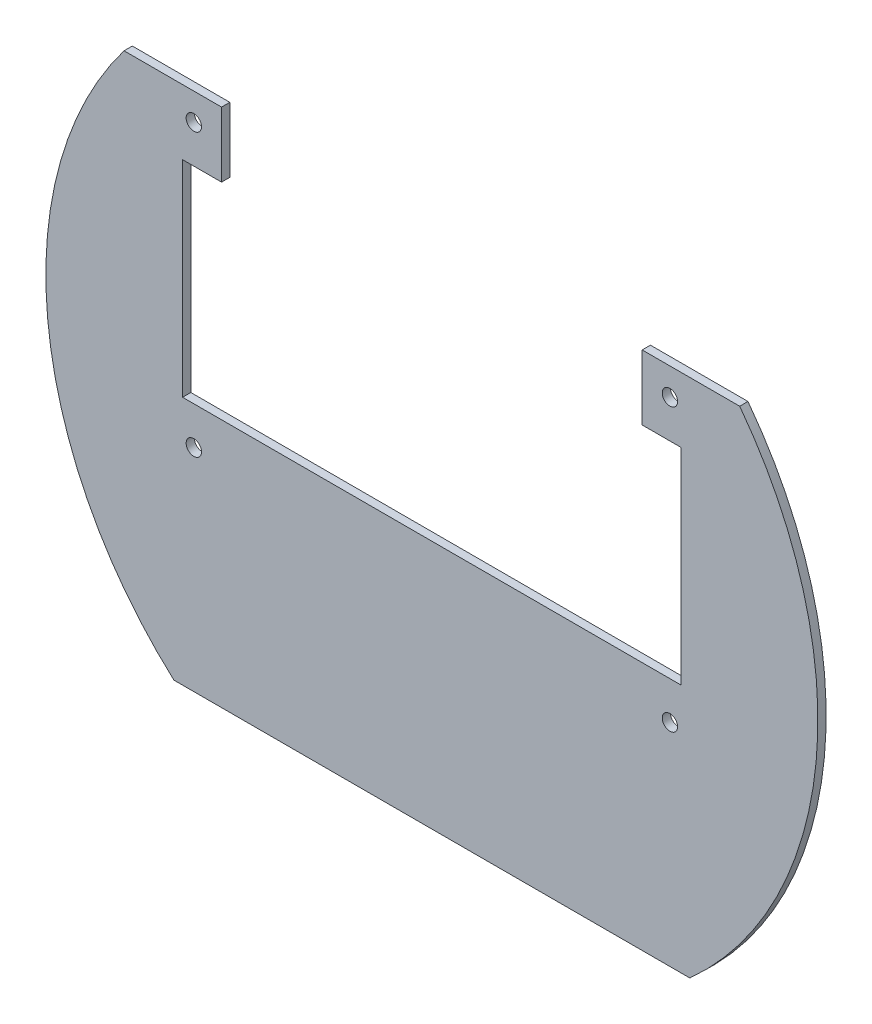
SolidWorks part; units mm, degrees
ref_plane "Front Plane" through (0, 0, 0) normal (0, 0, 1) x (1, 0, 0)
ref_plane "Top Plane" through (0, 0, 0) normal (0, 1, 0) x (1, 0, 0)
ref_plane "Right Plane" through (0, 0, 0) normal (1, 0, 0) x (0, 0, -1)
sketch "Sketch1" plane through (0, 0, 0) normal (0, 0, 1) x (1, 0, 0)
  line L0 (48.7, 32.8) -> (41.08, 32.8)
  line L1 (-46.5, -14.8) -> (46.5, -14.8) construction
  line L2 (-46.5, -14.8) -> (-46.5, 40.2) construction
  line L3 (-46.5, 40.2) -> (46.5, 40.2) construction
  line L4 (46.5, -14.8) -> (46.5, 40.2) construction
  line L5 (-46.5, -14.8) -> (46.5, 40.2) construction
  line L6 (-46.5, 40.2) -> (46.5, -14.8) construction
  line L7 (-48.7, -7.4) -> (48.7, -7.4) construction
  line L8 (-48.7, -7.4) -> (-48.7, 32.8) construction
  line L9 (-48.7, 32.8) -> (48.7, 32.8) construction
  line L10 (48.7, -7.4) -> (48.7, 32.8) construction
  line L11 (-48.7, -7.4) -> (48.7, 32.8) construction
  line L12 (-48.7, 32.8) -> (48.7, -7.4) construction
  line L13 (41.08, 32.8) -> (41.08, 45.5)
  line L14 (41.08, 45.5) -> (60.132, 45.5)
  line L15 (-48.7, 32.8) -> (-41.08, 32.8)
  line L16 (-41.08, 32.8) -> (-41.08, 45.5)
  line L17 (-41.08, 45.5) -> (-60.132, 45.5)
  line L18 (-48.7, 32.8) -> (-48.7, -7.4)
  line L19 (-48.7, -7.4) -> (48.7, -7.4)
  line L20 (48.7, -7.4) -> (48.7, 32.8)
  line L21 (-50.3874, -56.1) -> (50.3874, -56.1)
  arc A0 (-60.132, 45.5) -> (-50.3874, -56.1) centre (0, 0) ccw
  circle A1 centre (-46.5, 40.2) radius 1.5
  circle A2 centre (46.5, 40.2) radius 1.5
  circle A3 centre (46.5, -14.8) radius 1.5
  circle A4 centre (-46.5, -14.8) radius 1.5
  arc A5 (50.3874, -56.1) -> (60.132, 45.5) centre (0, 0) ccw
  point P3 (0, 12.7)
  point P8 (0, 12.7)
  dimension "D1" = 150.8125
  dimension "D7" = 3
  dimension "D2" = 12.7
  dimension "D3" = 55
  dimension "D4" = 93
  dimension "D5" = 97.4
  dimension "D6" = 40.2
  dimension "D8" = 7.62
  dimension "D9" = 7.62
  dimension "D10" = 12.7
  dimension "D11" = 12.7
  dimension "D12" = 101.6
extrude "Boss-Extrude1" add sketch "Sketch1" along normal blind 1.6129
